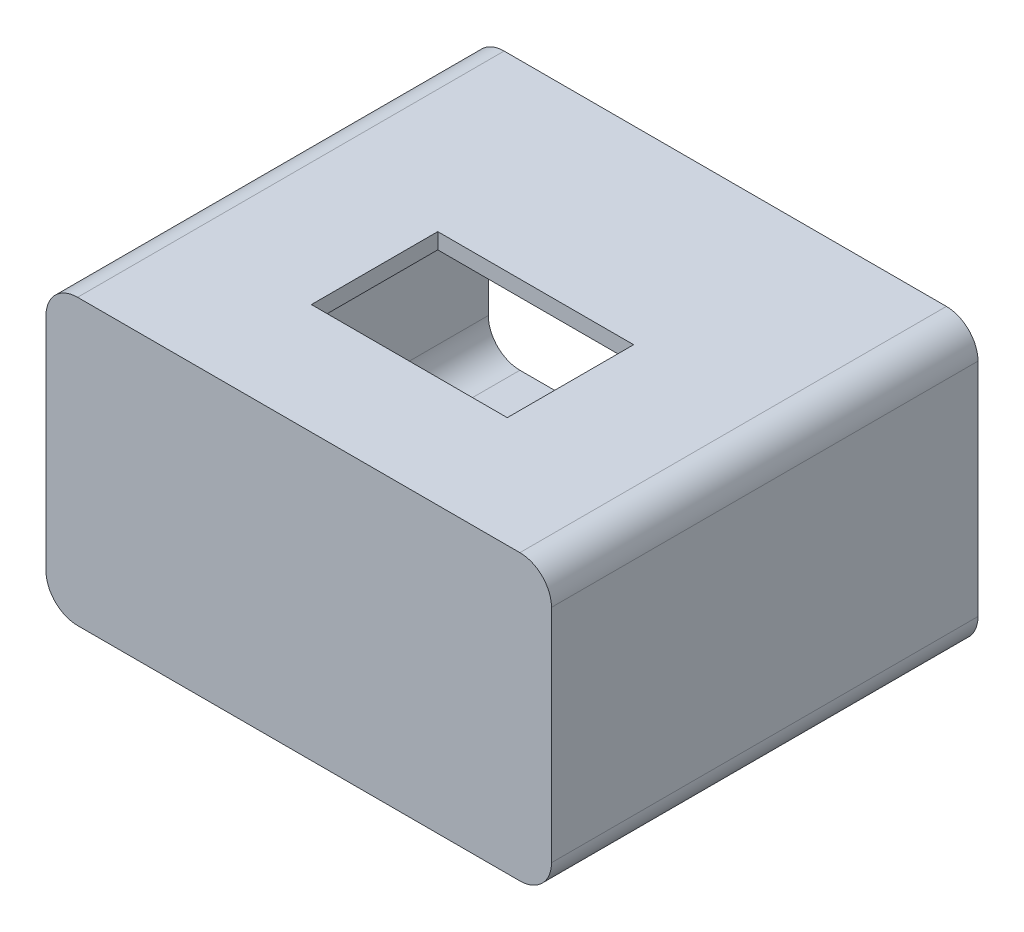
SolidWorks part; units mm, degrees
material "Hexcel AS4C (3000 Filaments)"
ref_plane "Front Plane" through (0, 0, 0) normal (0, 0, 1) x (1, 0, 0)
ref_plane "Top Plane" through (0, 0, 0) normal (0, 1, 0) x (1, 0, 0)
ref_plane "Right Plane" through (0, 0, 0) normal (1, 0, 0) x (0, 0, -1)
sketch "Sketch2" plane through (0, 0, 0) normal (0, 0, 1) x (1, 0, 0)
  line L0 (32.5, -20) -> (-32.5, -20) construction
  line L1 (37.5, 15) -> (37.5, -15) construction
  line L2 (-32.5, 20) -> (32.5, 20) construction
  line L3 (-37.5, -15) -> (-37.5, 15) construction
  line L4 (32.5, -20) -> (-32.5, -20)
  line L5 (37.5, 15) -> (37.5, -15)
  line L6 (-32.5, 20) -> (32.5, 20)
  line L7 (-37.5, -15) -> (-37.5, 15)
  line L9 (-35, -22.5) -> (35, -22.5)
  line L10 (-40, -17.5) -> (-40, 17.5)
  line L11 (-35, 22.5) -> (35, 22.5)
  line L12 (40, -17.5) -> (40, 17.5)
  line L13 (-40, -22.5) -> (40, 22.5) construction
  line L14 (-40, 22.5) -> (40, -22.5) construction
  arc A0 (-37.5, -15) -> (-32.5, -20) centre (-32.5, -15) ccw construction
  arc A1 (32.5, -20) -> (37.5, -15) centre (32.5, -15) ccw construction
  arc A2 (37.5, 15) -> (32.5, 20) centre (32.5, 15) ccw construction
  arc A3 (-32.5, 20) -> (-37.5, 15) centre (-32.5, 15) ccw construction
  circle A4 centre (-32.5, -15) radius 1.5 construction
  circle A5 centre (32.5, -15) radius 1.5 construction
  circle A6 centre (32.5, 15) radius 1.5 construction
  circle A7 centre (-32.5, 15) radius 1.5 construction
  arc A8 (-37.5, -15) -> (-32.5, -20) centre (-32.5, -15) ccw
  arc A9 (32.5, -20) -> (37.5, -15) centre (32.5, -15) ccw
  arc A10 (37.5, 15) -> (32.5, 20) centre (32.5, 15) ccw
  arc A11 (-32.5, 20) -> (-37.5, 15) centre (-32.5, 15) ccw
  circle A12 centre (-32.5, -15) radius 1.5
  circle A13 centre (32.5, -15) radius 1.5
  circle A14 centre (32.5, 15) radius 1.5
  circle A15 centre (-32.5, 15) radius 1.5
  arc A16 (35, 22.5) -> (40, 17.5) centre (35, 17.5) cw
  arc A17 (35, -22.5) -> (40, -17.5) centre (35, -17.5) ccw
  arc A18 (-35, -22.5) -> (-40, -17.5) centre (-35, -17.5) cw
  arc A19 (-40, 17.5) -> (-35, 22.5) centre (-35, 17.5) cw
  point P14 (0, 0)
  arc M3 (-32.5, 20) -> (-37.5, 15) centre (-32.5, 15) ccw
  line M4 (-37.5, 15) -> (-37.5, -15)
  arc M5 (-37.5, -15) -> (-32.5, -20) centre (-32.5, -15) ccw
  line M6 (-32.5, -20) -> (32.5, -20)
  arc M7 (32.5, -20) -> (37.5, -15) centre (32.5, -15) ccw
  line M8 (37.5, -15) -> (37.5, 15)
  arc M9 (37.5, 15) -> (32.5, 20) centre (32.5, 15) ccw
  line M10 (32.5, 20) -> (-32.5, 20)
  dimension "D3" = 5
  dimension "D1" = 2.5
  dimension "D2" = 2.5
extrude "Boss-Extrude1" add sketch "Sketch2" along normal blind 65 contours A19 L10 A18 L9 A17 L12 A16 L11 M3 M10 M9 M8 M7 M6 M5 M4
sketch "Sketch3" plane through (0, 0, 65) normal (0, 0, 1) x (1, 0, 0)
  line L4 (-40, 17.5) -> (-40, -17.5)
  line L5 (-35, -22.5) -> (35, -22.5)
  line L6 (40, -17.5) -> (40, 17.5)
  line L7 (35, 22.5) -> (-35, 22.5)
  line L8 (-40, 17.5) -> (-40, -17.5)
  line L9 (-35, -22.5) -> (35, -22.5)
  line L10 (40, -17.5) -> (40, 17.5)
  line L11 (35, 22.5) -> (-35, 22.5)
  arc A4 (-35, 22.5) -> (-40, 17.5) centre (-35, 17.5) ccw
  arc A5 (-40, -17.5) -> (-35, -22.5) centre (-35, -17.5) ccw
  arc A6 (35, -22.5) -> (40, -17.5) centre (35, -17.5) ccw
  arc A7 (40, 17.5) -> (35, 22.5) centre (35, 17.5) ccw
  arc A8 (-35, 22.5) -> (-40, 17.5) centre (-35, 17.5) ccw
  arc A9 (-40, -17.5) -> (-35, -22.5) centre (-35, -17.5) ccw
  arc A10 (35, -22.5) -> (40, -17.5) centre (35, -17.5) ccw
  arc A11 (40, 17.5) -> (35, 22.5) centre (35, 17.5) ccw
  dimension "D1" = 0
extrude "Boss-Extrude2" add sketch "Sketch3" along normal blind 2.5 contours A8 L8 A9 L9 A10 L10 A11 L11
sketch "Sketch4" plane through (0, 22.5, 0) normal (0, 1, 0) x (1, 0, 0)
  line L0 (-35, 0) -> (35, 0) construction
  line L1 (-15.5, -30) -> (15.5, -30)
  line L2 (-15.5, -30) -> (-15.5, -50)
  line L3 (-15.5, -50) -> (15.5, -50)
  line L4 (15.5, -30) -> (15.5, -50)
  line L5 (-15.5, -30) -> (15.5, -50) construction
  line L6 (-15.5, -50) -> (15.5, -30) construction
  point P0 (0, -40)
  dimension "D1" = 20
  dimension "D2" = 31
  dimension "D3" = 40
extrude "Cut-Extrude1" cut sketch "Sketch4" against normal up to next
